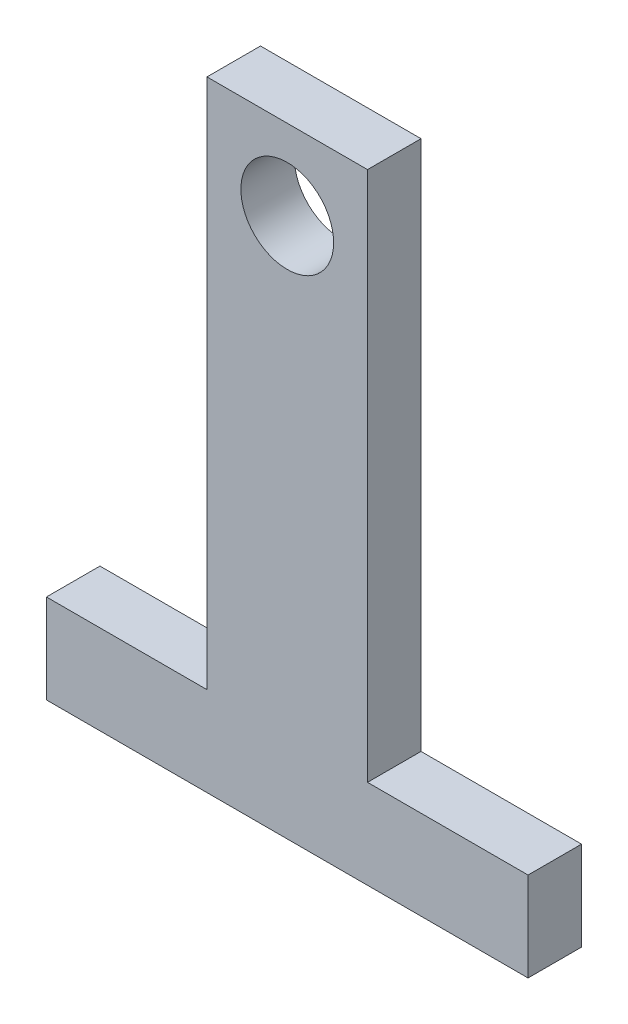
SolidWorks part; units mm, degrees
ref_plane "Plan de face" through (0, 0, 0) normal (0, 0, 1) x (1, 0, 0)
ref_plane "Plan de dessus" through (0, 0, 0) normal (0, 1, 0) x (1, 0, 0)
ref_plane "Plan de droite" through (0, 0, 0) normal (1, 0, 0) x (0, 0, -1)
sketch "Esquisse1" plane through (0, 0, 0) normal (0, 0, 1) x (1, 0, 0)
  line L0 (-9, 0) -> (-18, 0)
  line L1 (-18, 0) -> (-18, -5)
  line L2 (0, 0) -> (0, 29.75)
  line L3 (0, 29.75) -> (-9, 29.75)
  line L4 (-9, 0) -> (-9, 29.75)
  line L5 (-18, -5) -> (9, -5)
  line L6 (9, -5) -> (9, 0)
  line L7 (9, 0) -> (0, 0)
  circle A0 centre (-4.5, 25.25) radius 2.6
  dimension "D4" = 5.2
  dimension "D5" = 4.5
  dimension "D6" = 4.5
  dimension "D1" = 30.25
  dimension "D2" = 9
  dimension "D3" = 5
  dimension "D7" = 9
  dimension "D8" = 9
extrude "Boss.-Extru.1" add sketch "Esquisse1" along normal blind 3
